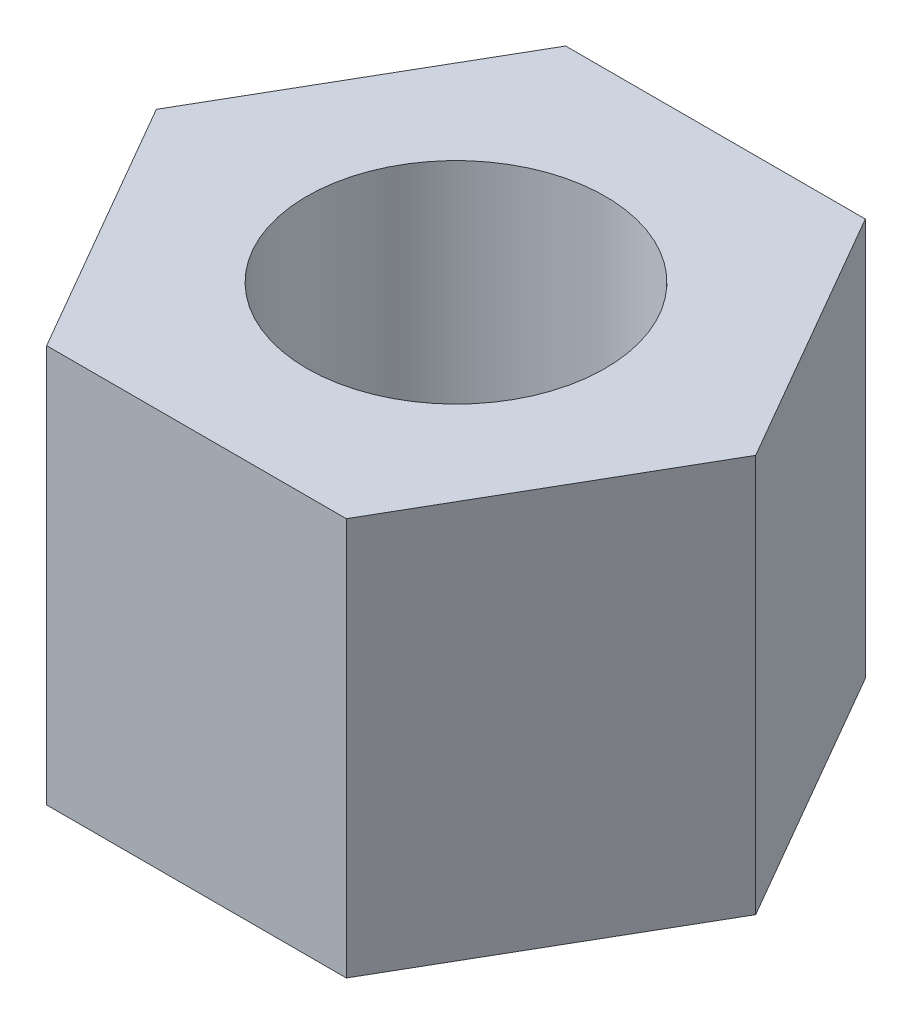
SolidWorks part; units mm, degrees
ref_plane "Front Plane" through (0, 0, 0) normal (0, 0, 1) x (1, 0, 0)
ref_plane "Top Plane" through (0, 0, 0) normal (0, 1, 0) x (1, 0, 0)
ref_plane "Right Plane" through (0, 0, 0) normal (1, 0, 0) x (0, 0, -1)
sketch "Sketch1" plane through (0, 0, 0) normal (0, 1, 0) x (1, 0, 0)
  line L1 (3.0134, 0) -> (1.5067, 2.6097)
  line L2 (1.5067, 2.6097) -> (-1.5067, 2.6097)
  line L3 (-1.5067, 2.6097) -> (-3.0134, 0)
  line L4 (-3.0134, 0) -> (-1.5067, -2.6097)
  line L5 (-1.5067, -2.6097) -> (1.5067, -2.6097)
  line L6 (1.5067, -2.6097) -> (3.0134, 0)
  circle A0 centre (0, 0) radius 1.5
  circle A1 centre (0, 0) radius 2.6097 construction
extrude "Boss-Extrude1" add sketch "Sketch1" along normal blind 4
